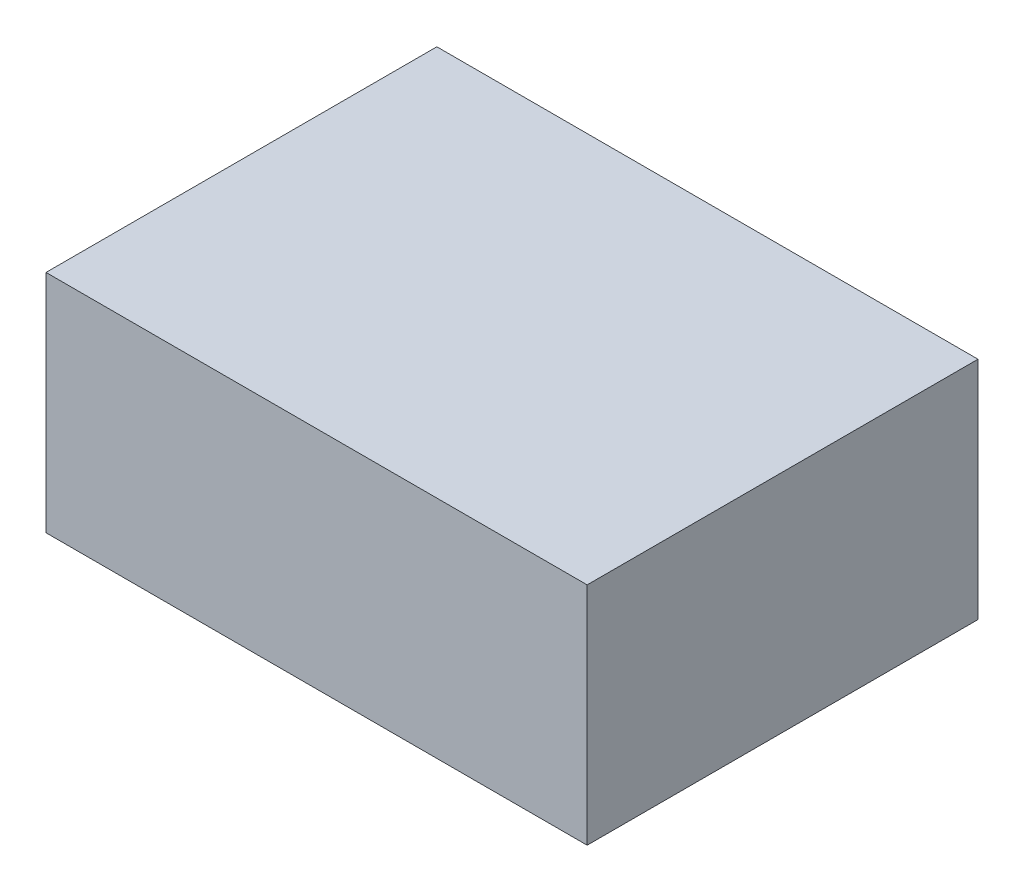
SolidWorks part; units mm, degrees
ref_plane "Front Plane" through (0, 0, 0) normal (0, 0, 1) x (1, 0, 0)
ref_plane "Top Plane" through (0, 0, 0) normal (0, 1, 0) x (1, 0, 0)
ref_plane "Right Plane" through (0, 0, 0) normal (1, 0, 0) x (0, 0, -1)
sketch "Sketch1" plane through (0, 0, 0) normal (0, 1, 0) x (1, 0, 0)
  line L1 (-22.86, -16.51) -> (22.86, -16.51)
  line L2 (-22.86, -16.51) -> (-22.86, 16.51)
  line L3 (-22.86, 16.51) -> (22.86, 16.51)
  line L4 (22.86, -16.51) -> (22.86, 16.51)
  line L5 (-22.86, -16.51) -> (22.86, 16.51) construction
  line L6 (-22.86, 16.51) -> (22.86, -16.51) construction
  point P0 (0, 0)
  dimension "D1" = 45.72
  dimension "D2" = 33.02
extrude "Boss-Extrude1" add sketch "Sketch1" along normal blind 19.05
